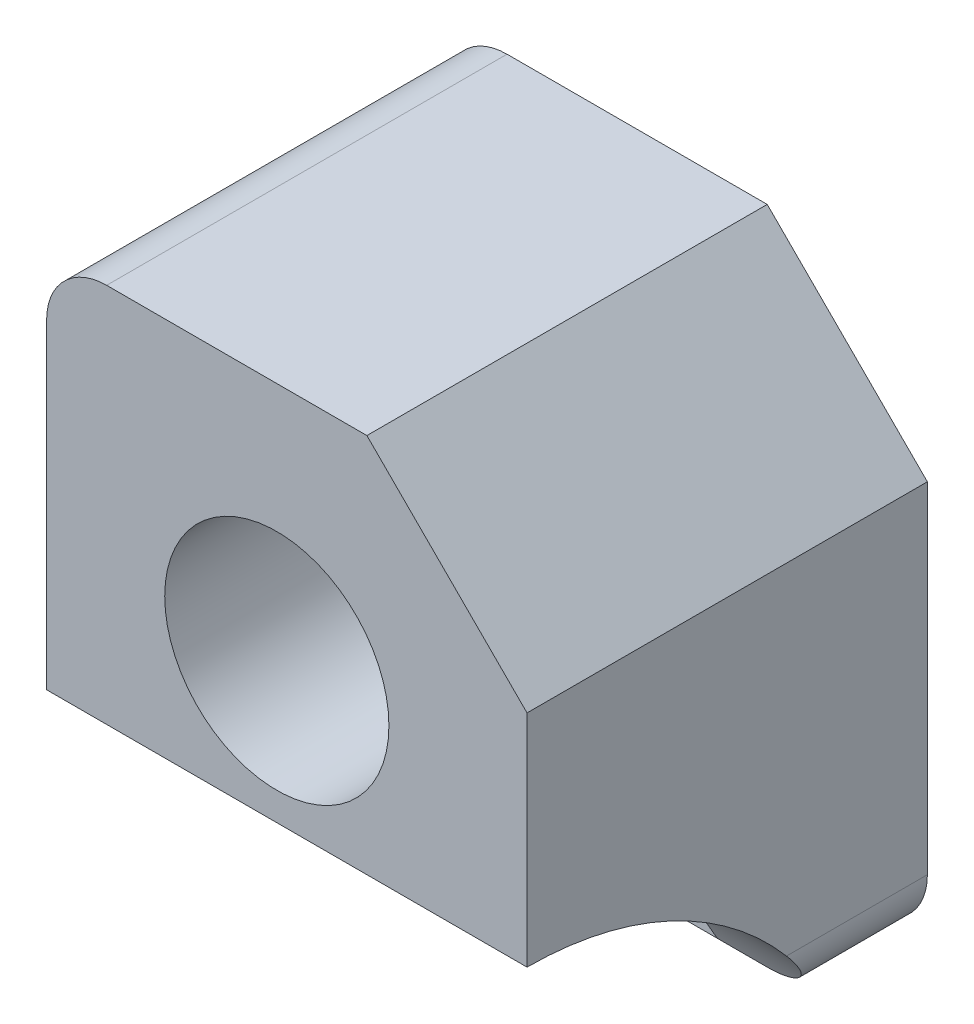
SolidWorks part; units mm, degrees
material "ABS"
ref_plane "Front Plane" through (0, 0, 0) normal (0, 0, 1) x (1, 0, 0)
ref_plane "Top Plane" through (0, 0, 0) normal (0, 1, 0) x (1, 0, 0)
ref_plane "Right Plane" through (0, 0, 0) normal (1, 0, 0) x (0, 0, -1)
sketch "Sketch1" plane through (0, 0, 0) normal (0, 0, 1) x (1, 0, 0)
  line L0 (16, 28) -> (24, 20)
  line L1 (0, 0) -> (24, 0)
  line L2 (0, 0) -> (0, 28)
  line L3 (0, 28) -> (24, 28)
  line L4 (24, 0) -> (24, 28)
  circle A0 centre (14, 4) radius 2
  circle A1 centre (4, 4) radius 2
  circle A2 centre (11.5, 16) radius 5.6
  dimension "D1" = 4
  dimension "D9" = 11.2
  dimension "D2" = 10
  dimension "D3" = 4
  dimension "D4" = 4
  dimension "D5" = 28
  dimension "D6" = 24
  dimension "D7" = 8
  dimension "D8" = 8
  dimension "D10" = 11.5
  dimension "D11" = 12
extrude "Boss-Extrude1" add sketch "Sketch1" along normal blind 20 contours L1 L4 L0 L3 L2 A2 A1 A0
sketch "Sketch2" plane through (0, 0, 0) normal (-1, 0, 0) x (0, 0, 1)
  line L0 (20, 9) -> (20, 0)
  line L1 (20, 0) -> (20, 28) construction
  line L2 (20, 0) -> (5, 0)
  line L3 (20, 0) -> (0, 0) construction
  line L4 (20, 9) -> (26.0151, 9) construction
  arc A0 (20, 9) -> (5, 0) centre (20, -8) ccw
  dimension "D1" = 9
  dimension "D2" = 5
extrude "Cut-Extrude1" cut sketch "Sketch2" against normal blind 30
sketch "Sketch3" plane through (0, 0, 20) normal (0, 0, 1) x (1, 0, 0)
  line L1 (18.5, 4) -> (9.5, 4)
  line L2 (18.5, 4) -> (18.5, -0.5)
  line L3 (18.5, -0.5) -> (9.5, -0.5)
  line L4 (9.5, 4) -> (9.5, -0.5)
  line L5 (8.5, 4) -> (0, 4)
  line L6 (8.5, 4) -> (8.5, -0.5)
  line L7 (8.5, -0.5) -> (0, -0.5)
  line L8 (0, 4) -> (0, -0.5)
  circle A0 centre (14, 4) radius 4.5
  circle A1 centre (4, 4) radius 4.5
  dimension "D4" = 9
  dimension "D5" = 9
  dimension "D1" = 4
  dimension "D2" = 14
  dimension "D3" = 4
extrude "Cut-Extrude2" cut sketch "Sketch3" against normal blind 15 contours L1 A0 | L1 A0 | A0 L4 L3 | A0 L3 L2 | L8 A1 L5 | A1 L7 L6 | A1 L8 L7 | L5 A1 L8
fillet "Fillet1" radius 3 3 edges at (0, 28, 10) (24, 0, 2.5) (0, 0, 2.5)
